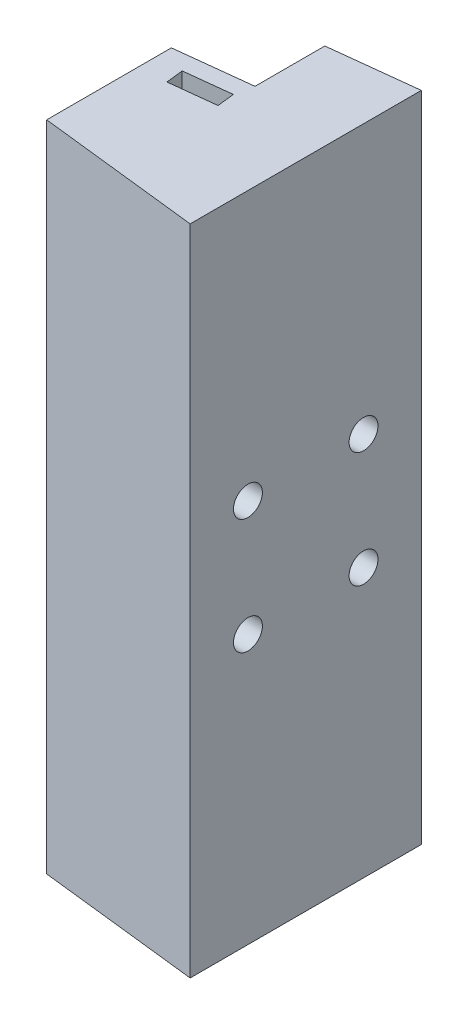
SolidWorks part; units mm, degrees
ref_plane "Front Plane" through (0, 0, 0) normal (0, 0, 1) x (1, 0, 0)
ref_plane "Top Plane" through (0, 0, 0) normal (0, 1, 0) x (1, 0, 0)
ref_plane "Right Plane" through (0, 0, 0) normal (1, 0, 0) x (0, 0, -1)
sketch "Sketch1" plane through (0, 0, 0) normal (0, 1, 0) x (1, 0, 0)
  line L0 (0, 0) -> (-176.3587, -20) construction
  line L1 (-176.3587, -20) -> (0, -40) construction
  line L2 (0, -40) -> (0, 0) construction
  line L3 (0, 0) -> (-28, -3.1753)
  line L6 (0, -40) -> (0, 0)
  line L7 (0, -20) -> (-176.3587, -20) construction
  line L8 (0, -40) -> (-28, -36.8247)
  line L9 (-28, -36.8247) -> (-28, -3.1753)
  dimension "D1" = 40
  dimension "D2" = 12.94
  dimension "D3" = 28
extrude "Boss-Extrude1" add sketch "Sketch1" along normal mid plane 113
sketch "Sketch2" plane through (0, 0, 0) normal (1, 0, 0) x (0, 0, -1)
  line L0 (-30, 10) -> (-30, -10) construction
  line L1 (-30, -10) -> (-10, -10) construction
  line L2 (-10, -10) -> (-10, 10) construction
  line L3 (-10, 10) -> (-30, 10) construction
  line L5 (0, 0) -> (-10, 0) construction
  line L6 (-40, 56.5) -> (-40, -56.5) construction
  circle A0 centre (-10, 10) radius 2.5
  circle A1 centre (-10, -10) radius 2.5
  circle A2 centre (-30, 10) radius 2.5
  circle A3 centre (-30, -10) radius 2.5
  point P13 (-40, 0)
  dimension "D1" = 5
  dimension "D2" = 5
  dimension "D3" = 5
  dimension "D4" = 5
  dimension "D5" = 20
  dimension "D6" = 20
  dimension "D7" = 10
extrude "Cut-Extrude1" cut sketch "Sketch2" against normal blind 20
sketch "Sketch5" plane through (-28, 0, 0) normal (-1, 0, 0) x (0, 0, 1)
  circle A0 centre (30, 10) radius 5
  circle A1 centre (30, -10) radius 5
  circle A2 centre (10, -10) radius 5
  circle A3 centre (10, 10) radius 5
  dimension "D1" = 10
  dimension "D2" = 10
  dimension "D3" = 10
  dimension "D4" = 10
extrude "Cut-Extrude4" cut sketch "Sketch5" against normal blind 22
sketch "Sketch6" plane through (0, -56.5, 0) normal (0, -1, 0) x (1, 0, 0)
  line L0 (-15, 1.7011) -> (-15, 13.778)
  line L1 (0, 0) -> (-28, 3.1753) construction
  line L2 (-15, 13.778) -> (-28, 15.2523)
  line L3 (-28, 3.1753) -> (-28, 36.8247) construction
  line L4 (-28, 15.2523) -> (-28, 3.1753)
  line L5 (-28, 3.1753) -> (-15, 1.7011)
  line L6 (0, 40) -> (0, 0) construction
  dimension "D1" = 15
  dimension "D2" = 12
extrude "Cut-Extrude5" cut sketch "Sketch6" against normal blind 126 contours L5 L0 L2 L4
sketch "Sketch7" plane through (1.3522, 0, 11.9236) normal (-0.1127, 0, -0.9936) x (-0.9936, 0, 0.1127)
  line L0 (16.457, 56.5) -> (16.457, 13.2752) construction
  line L1 (29.5403, 56.5) -> (16.457, 56.5) construction
  line L2 (16.457, -56.5) -> (29.5403, -56.5) construction
  line L3 (16.457, -13.2752) -> (16.457, -56.5) construction
  circle A0 centre (21.457, -51.5) radius 2
  circle A1 centre (21.457, 51.5) radius 2
  dimension "D1" = 4
  dimension "D2" = 4
  dimension "D3" = 5
  dimension "D4" = 5
  dimension "D5" = 5
  dimension "D6" = 5
extrude "Cut-Extrude6" cut sketch "Sketch7" against normal blind 6
sketch "Sketch9" plane through (2.0283, 0, 17.8854) normal (-0.1127, 0, -0.9936) x (-0.9936, 0, 0.1127)
  line L0 (17.457, -51.5) -> (17.457, -56.5)
  line L1 (17.457, -56.5) -> (25.457, -56.5)
  line L2 (25.457, -56.5) -> (25.457, -51.5)
  line L3 (17.457, 56.5) -> (17.457, 51.5)
  line L4 (17.457, 56.5) -> (25.457, 56.5)
  line L5 (25.457, 56.5) -> (25.457, 51.5)
  line L6 (29.5403, 56.5) -> (16.457, 56.5) construction
  line L7 (16.457, -56.5) -> (29.5403, -56.5) construction
  arc A0 (25.457, -51.5) -> (17.457, -51.5) centre (21.457, -51.5) ccw
  arc A1 (17.457, 51.5) -> (25.457, 51.5) centre (21.457, 51.5) ccw
  point P1 (25.4936, 56.2616)
  point P9 (17.4936, 51.5)
  point P11 (17.4936, 51.5)
  point P12 (0, 0)
  dimension "D1" = 8
  dimension "D2" = 8
extrude "Cut-Extrude7" cut sketch "Sketch9" along normal blind 3
sketch "Sketch10" plane through (2.0283, 0, 17.8854) normal (-0.1127, 0, -0.9936) x (-0.9936, 0, 0.1127)
  circle A0 centre (21.457, 51.5) radius 2
  circle A1 centre (21.457, -51.5) radius 2
  dimension "D1" = 4
  dimension "D2" = 4
extrude "Cut-Extrude8" cut sketch "Sketch10" against normal blind 2
